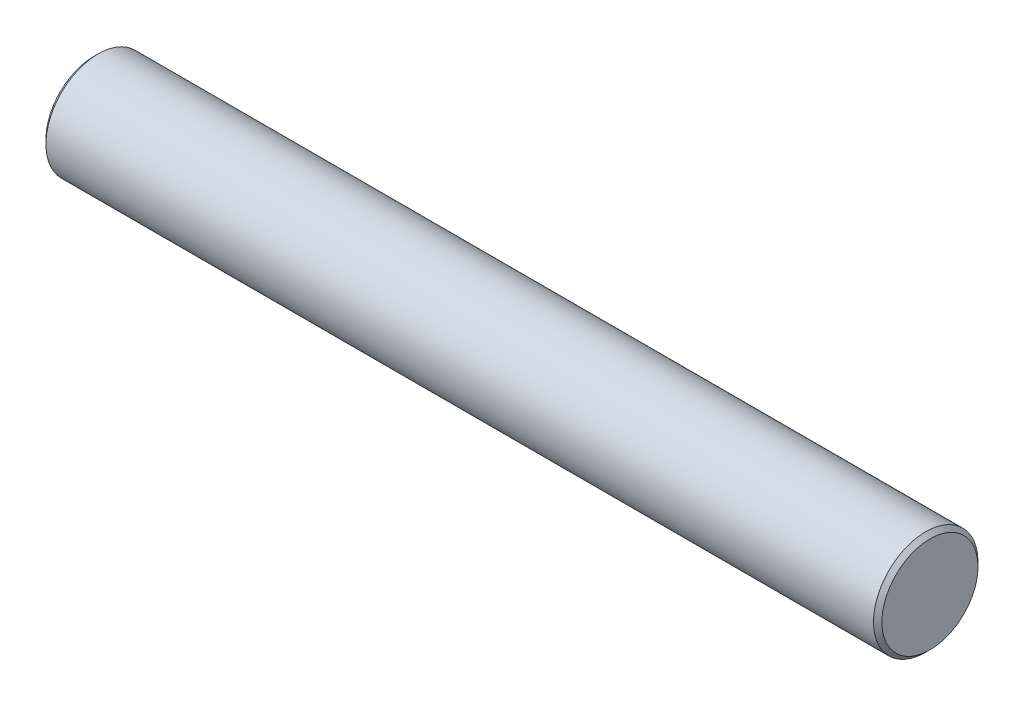
SolidWorks part; units mm, degrees
ref_plane "Front Plane" through (0, 0, 0) normal (0, 0, 1) x (1, 0, 0)
ref_plane "Top Plane" through (0, 0, 0) normal (0, 1, 0) x (1, 0, 0)
ref_plane "Right Plane" through (0, 0, 0) normal (1, 0, 0) x (0, 0, -1)
sketch "Sketch1" plane through (0, 0, 0) normal (1, 0, 0) x (0, 0, -1)
  circle A0 centre (0, 0) radius 3.175
  dimension "D1" = 6.35
extrude "Boss-Extrude1" add sketch "Sketch1" against normal blind 50.8
chamfer "Chamfer1" distance 0.254 angle 45 2 edges at (-50.8, 0, -3.175) (0, 0, -3.175)
